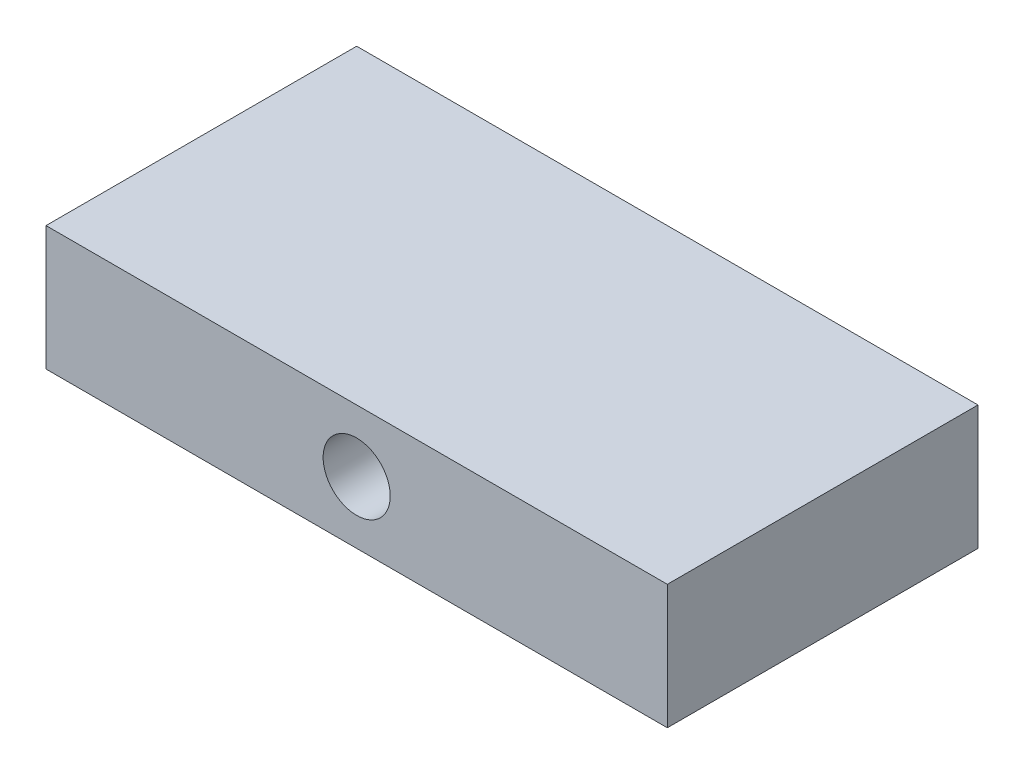
SolidWorks part; units mm, degrees
material "NEOPRENE"
ref_plane "Front Plane" through (0, 0, 0) normal (0, 0, 1) x (1, 0, 0)
ref_plane "Top Plane" through (0, 0, 0) normal (0, 1, 0) x (1, 0, 0)
ref_plane "Right Plane" through (0, 0, 0) normal (1, 0, 0) x (0, 0, -1)
sketch "Sketch1" plane through (0, 0, 0) normal (0, 1, 0) x (1, 0, 0)
  line L1 (-63.5, 31.75) -> (63.5, 31.75)
  line L2 (-63.5, 31.75) -> (-63.5, -31.75)
  line L3 (-63.5, -31.75) -> (63.5, -31.75)
  line L4 (63.5, 31.75) -> (63.5, -31.75)
  line L5 (-63.5, 31.75) -> (63.5, -31.75) construction
  line L6 (-63.5, -31.75) -> (63.5, 31.75) construction
  point P0 (0, 0)
  dimension "D1" = 127
  dimension "D2" = 63.5
extrude "Boss-Extrude1" add sketch "Sketch1" along normal blind 25.4
sketch "Sketch2" plane through (0, 0, 31.75) normal (0, 0, 1) x (1, 0, 0)
  line L0 (-63.5, 12.7) -> (0, 12.7) construction
  line L1 (-63.5, 25.4) -> (-63.5, 0) construction
  circle A0 centre (0, 12.7) radius 6.858
  dimension "D1" = 13.716
extrude "Cut-Extrude1" cut sketch "Sketch2" against normal blind 19.05
sketch "Sketch3" plane through (0, 0, -31.75) normal (0, 0, -1) x (-1, 0, 0)
  line L0 (0, 0) -> (0, 12.7) construction
  line L1 (0, 12.7) -> (25.4, 12.7) construction
  circle A0 centre (25.4, 12.7) radius 6.858
  circle A1 centre (-25.4, 12.7) radius 6.858
  dimension "D3" = 13.716
  dimension "D1" = 12.7
  dimension "D2" = 25.4
extrude "Cut-Extrude2" cut sketch "Sketch3" against normal blind 19.05
